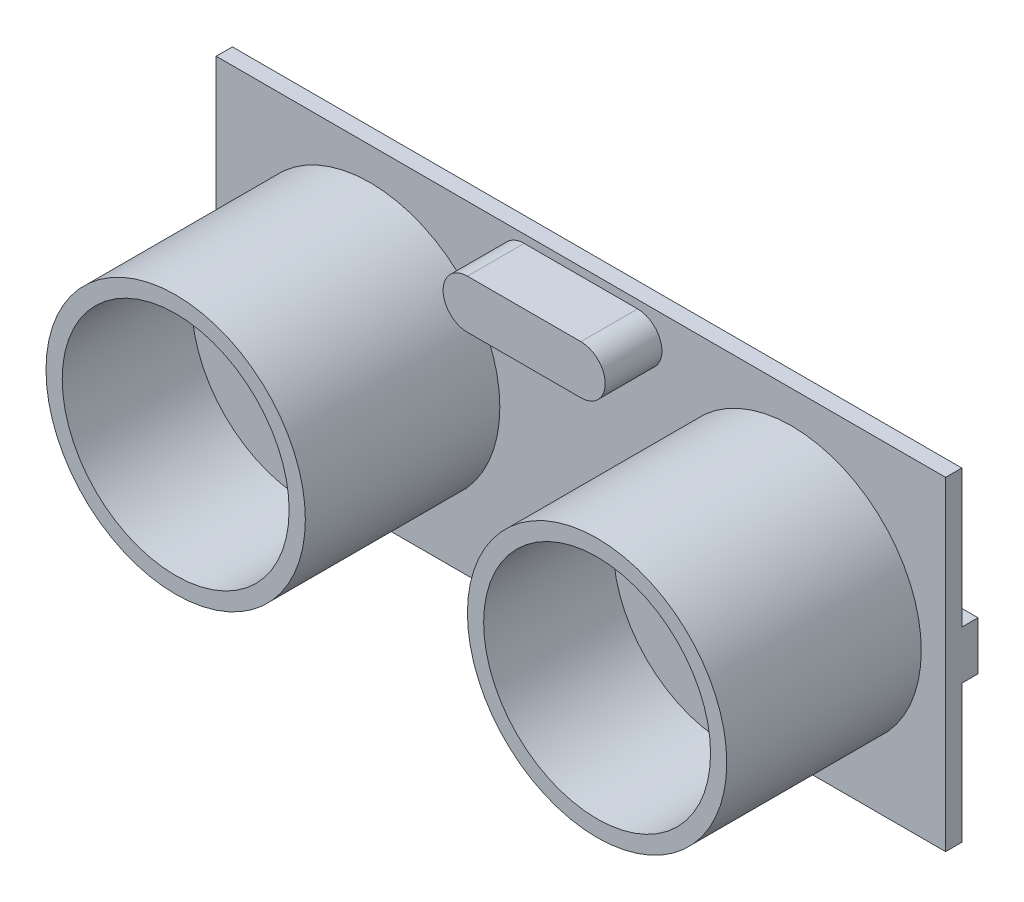
SolidWorks part; units mm, degrees
ref_plane "Front Plane" through (0, 0, 0) normal (0, 0, 1) x (1, 0, 0)
ref_plane "Top Plane" through (0, 0, 0) normal (0, 1, 0) x (1, 0, 0)
ref_plane "Right Plane" through (0, 0, 0) normal (1, 0, 0) x (0, 0, -1)
sketch "Sketch1" plane through (0, 0, 0) normal (0, 0, 1) x (1, 0, 0)
  line L1 (-22.5, -10) -> (22.5, -10)
  line L2 (-22.5, -10) -> (-22.5, 10)
  line L3 (-22.5, 10) -> (22.5, 10)
  line L4 (22.5, -10) -> (22.5, 10)
  line L5 (-22.5, -10) -> (22.5, 10) construction
  line L6 (-22.5, 10) -> (22.5, -10) construction
  point P0 (0, 0)
  dimension "D1" = 45
  dimension "D2" = 20
extrude "Boss-Extrude1" add sketch "Sketch1" along normal blind 1
sketch "Sketch2" plane through (0, 0, 1) normal (0, 0, 1) x (1, 0, 0)
  line L0 (0, -12.3779) -> (0, 14.1718) construction
  line L1 (22.5, -10) -> (22.5, 10) construction
  line L2 (-13, 0) -> (13, 0) construction
  circle A0 centre (13, 0) radius 8
  circle A1 centre (-13, 0) radius 8
  dimension "D1" = 16
  dimension "D2" = 9.5
extrude "Boss-Extrude2" add sketch "Sketch2" along normal blind 12
sketch "Sketch3" plane through (0, 0, 1) normal (0, 0, 1) x (1, 0, 0)
  line L4 (-7.6779, 0) -> (14.3512, 0) construction
  line L5 (-3.5, 8) -> (3.5, 8) construction
  line L6 (-3.5, 6.5) -> (3.5, 6.5)
  line L7 (-3.5, 9.5) -> (3.5, 9.5)
  arc A2 (-3.5, 6.5) -> (-3.5, 9.5) centre (-3.5, 8) cw
  arc A3 (3.5, 9.5) -> (3.5, 6.5) centre (3.5, 8) cw
  point P14 (0, 8)
extrude "Boss-Extrude4" add sketch "Sketch3" along normal blind 3.5 contours L6 A3 L7 A2
sketch "Sketch4" plane through (0, 0, 13) normal (0, 0, 1) x (1, 0, 0)
  line L0 (0, -3.9107) -> (0, 13.813) construction
  line L1 (22.5, -10) -> (22.5, 10) construction
  circle A1 centre (-13, 0) radius 7
  circle A2 centre (13, 0) radius 7
  dimension "D1" = 9.5
extrude "Cut-Extrude1" cut sketch "Sketch4" against normal blind 8
sketch "Sketch8" plane through (0, 0, 0) normal (0, 0, -1) x (-1, 0, 0)
  line L0 (-22.5, -10) -> (-22.5, 10) construction
  line L1 (-3, 1.5) -> (3, 1.5)
  line L2 (-3, 1.5) -> (-3, -1.5)
  line L3 (-3, -1.5) -> (3, -1.5)
  line L4 (3, 1.5) -> (3, -1.5)
  line L5 (-3, 1.5) -> (3, -1.5) construction
  line L6 (-3, -1.5) -> (3, 1.5) construction
  line L7 (-22.5, 1.5) -> (-16.5, 1.5)
  line L8 (-22.5, 1.5) -> (-22.5, -1.5)
  line L9 (-22.5, -1.5) -> (-16.5, -1.5)
  line L10 (-16.5, 1.5) -> (-16.5, -1.5)
  line L11 (-22.5, 1.5) -> (-16.5, -1.5) construction
  line L12 (-22.5, -1.5) -> (-16.5, 1.5) construction
  line L14 (16.9494, -3.25) -> (19.9494, -3.25)
  line L15 (16.9494, -3.25) -> (16.9494, 3.25)
  line L16 (16.9494, 3.25) -> (19.9494, 3.25)
  line L17 (19.9494, -3.25) -> (19.9494, 3.25)
  line L18 (16.9494, -3.25) -> (19.9494, 3.25) construction
  line L19 (16.9494, 3.25) -> (19.9494, -3.25) construction
  point P0 (0, 0)
  point P6 (-19.5, 0)
  point P13 (18.4494, 0)
  dimension "D1" = 6
  dimension "D2" = 3
  dimension "D3" = 3
  dimension "D4" = 6
  dimension "D5" = 3
  dimension "D6" = 6.5
  dimension "D7" = 3
extrude "Boss-Extrude5" add sketch "Sketch8" along normal blind 1
sketch "Sketch9" plane through (0, 0, 0) normal (0, 0, -1) x (-1, 0, 0)
  line L0 (22.5, -10) -> (-22.5, -10) construction
  line L1 (-6.35, -5) -> (6.35, -5)
  line L2 (-6.35, -5) -> (-6.35, -10)
  line L3 (-6.35, -10) -> (6.35, -10)
  line L4 (6.35, -5) -> (6.35, -10)
  line L5 (-6.35, -5) -> (6.35, -10) construction
  line L6 (-6.35, -10) -> (6.35, -5) construction
  point P0 (0, -7.5)
  dimension "D1" = 5
  dimension "D2" = 12.7
  dimension "D3" = 0
extrude "Boss-Extrude6" add sketch "Sketch9" along normal blind 4
sketch "Sketch10" plane through (0, -10, 0) normal (0, -1, 0) x (1, 0, 0)
  line L0 (-6.35, -4) -> (-6.35, 0) construction
  circle A0 centre (-3.85, -2.098) radius 0.5
  circle A1 centre (-1.31, -2.098) radius 0.5
  circle A2 centre (1.23, -2.098) radius 0.5
  circle A3 centre (3.77, -2.098) radius 0.5
  dimension "D1" = 1
  dimension "D2" = 2.5
  dimension "D3" = 4
extrude "Boss-Extrude7" add sketch "Sketch10" along normal blind 8
